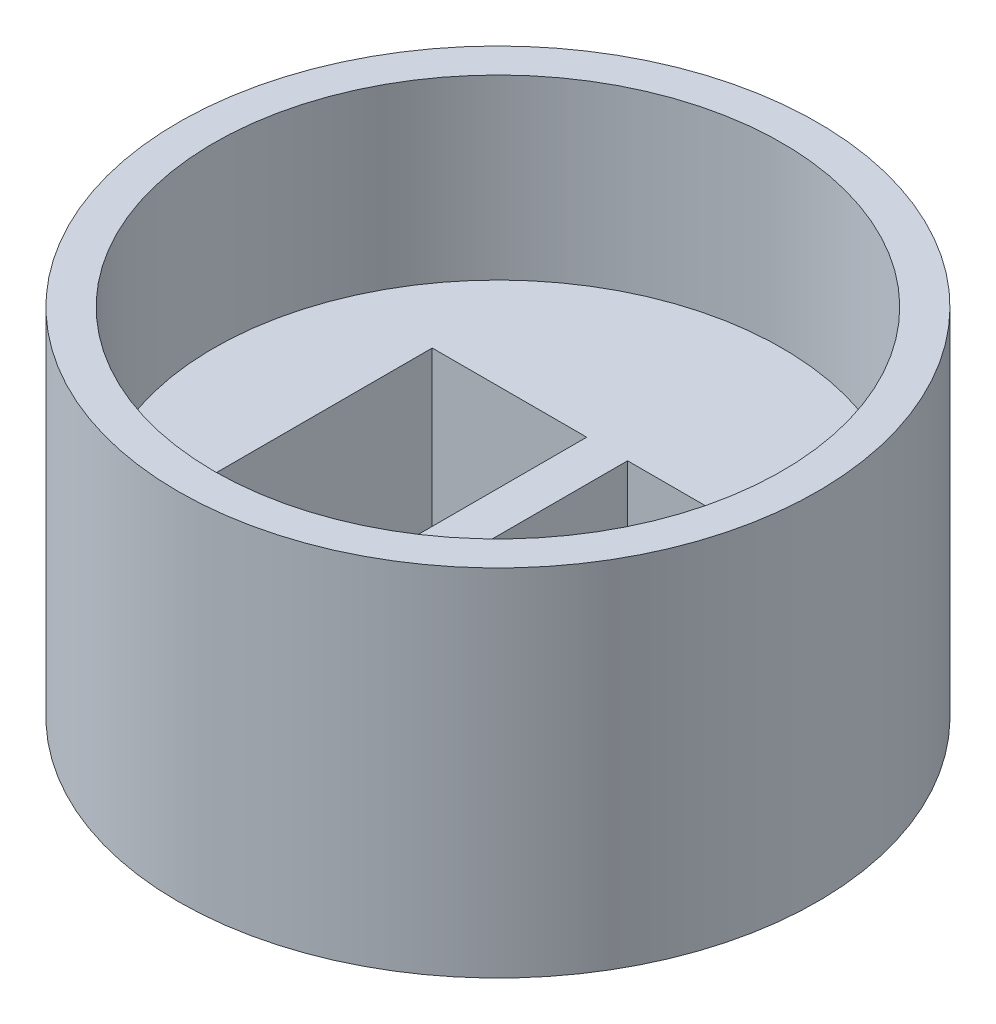
SolidWorks part; units mm, degrees
ref_plane "Front Plane" through (0, 0, 0) normal (0, 0, 1) x (1, 0, 0)
ref_plane "Top Plane" through (0, 0, 0) normal (0, 1, 0) x (1, 0, 0)
ref_plane "Right Plane" through (0, 0, 0) normal (1, 0, 0) x (0, 0, -1)
sketch "Sketch2" plane through (0, 0, 0) normal (0, 1, 0) x (1, 0, 0)
  circle A0 centre (0, 0) radius 9
  dimension "D1" = 18
extrude "Boss-Extrude2" add sketch "Sketch2" along normal blind 10
sketch "Sketch3" plane through (0, 10, 0) normal (0, 1, 0) x (1, 0, 0)
  circle A0 centre (0, 0) radius 8
  dimension "D1" = 16
extrude "Cut-Extrude1" cut sketch "Sketch3" against normal blind 5
sketch "Sketch4" plane through (0, 5, 0) normal (0, 1, 0) x (1, 0, 0)
  line L0 (-8, 0) -> (8, 0) construction
  line L2 (4.925, -3.075) -> (0.575, -3.075)
  line L3 (4.925, -3.075) -> (4.925, 3.075)
  line L4 (4.925, 3.075) -> (0.575, 3.075)
  line L5 (0.575, -3.075) -> (0.575, 3.075)
  line L6 (4.925, -3.075) -> (0.575, 3.075) construction
  line L7 (4.925, 3.075) -> (0.575, -3.075) construction
  line L8 (-4.925, 3.075) -> (-0.575, 3.075)
  line L9 (-4.925, 3.075) -> (-4.925, -3.075)
  line L10 (-4.925, -3.075) -> (-0.575, -3.075)
  line L11 (-0.575, 3.075) -> (-0.575, -3.075)
  line L12 (-4.925, 3.075) -> (-0.575, -3.075) construction
  line L13 (-4.925, -3.075) -> (-0.575, 3.075) construction
  circle A0 centre (0, 0) radius 8 construction
  circle A1 centre (0, 0) radius 8 construction
  point P7 (2.75, 0)
  point P12 (-2.75, 0)
  dimension "D1" = 4.35
  dimension "D2" = 6.15
  dimension "D3" = 4.35
  dimension "D4" = 6.15
  dimension "D5" = 2.75
  dimension "D6" = 2.75
extrude "Cut-Extrude2" cut sketch "Sketch4" against normal through all
